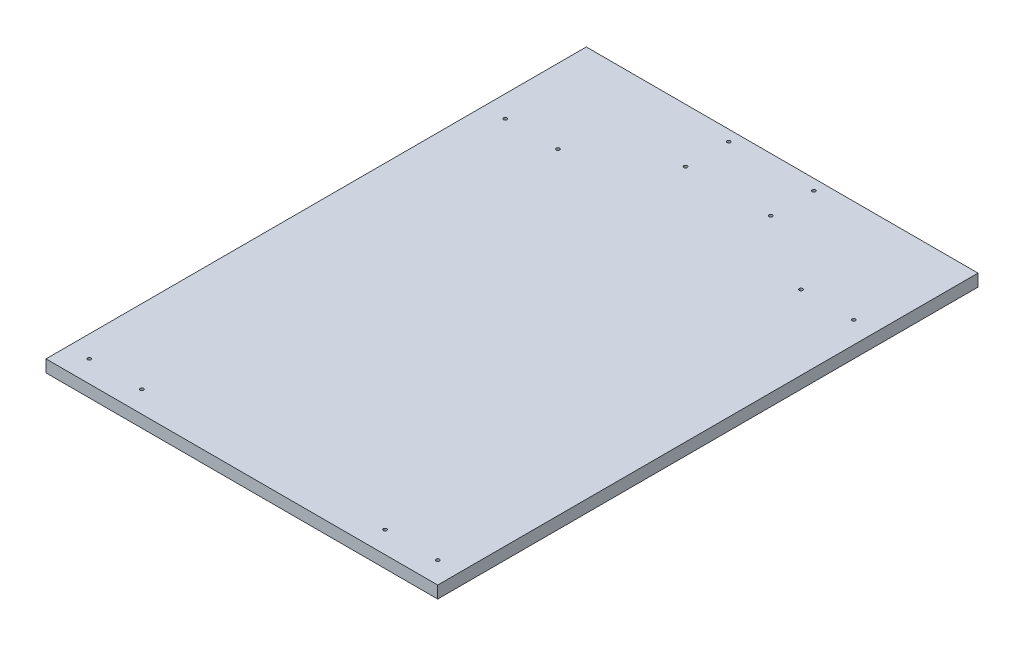
SolidWorks part; units mm, degrees
material "PBT General Purpose"
ref_plane "Front Plane" through (0, 0, 0) normal (0, 0, 1) x (1, 0, 0)
ref_plane "Top Plane" through (0, 0, 0) normal (0, 1, 0) x (1, 0, 0)
ref_plane "Right Plane" through (0, 0, 0) normal (1, 0, 0) x (0, 0, -1)
sketch "Sketch1" plane through (0, 0, 0) normal (0, 1, 0) x (1, 0, 0)
  line L1 (0, 0) -> (290, 0)
  line L2 (0, 0) -> (0, 400)
  line L3 (0, 400) -> (290, 400)
  line L4 (290, 0) -> (290, 400)
  dimension "D1" = 400
  dimension "D2" = 290
extrude "Boss-Extrude1" add sketch "Sketch1" along normal blind 9
sketch "Sketch2" plane through (0, 9, 0) normal (0, 1, 0) x (1, 0, 0)
  circle A0 centre (16, 16) radius 1.25
  circle A1 centre (55, 16) radius 1.25
  circle A2 centre (235, 16) radius 1.25
  circle A3 centre (274, 16) radius 1.25
  circle A4 centre (16, 324) radius 1.25
  circle A5 centre (55, 324) radius 1.25
  circle A6 centre (274, 324) radius 1.25
  circle A7 centre (235, 324) radius 1.25
  circle A8 centre (113.5, 392) radius 1.25
  circle A9 centre (113.5, 360) radius 1.25
  circle A10 centre (176.5, 360) radius 1.25
  circle A11 centre (176.5, 392) radius 1.25
extrude "Cut-Extrude1" cut sketch "Sketch2" against normal through all
